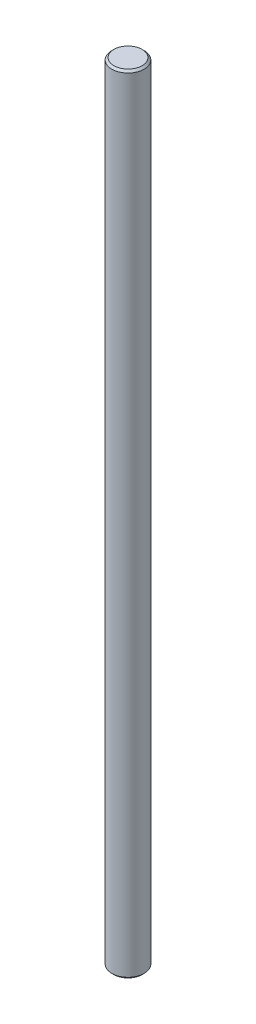
SolidWorks part; units mm, degrees
ref_plane "Front Plane" through (0, 0, 0) normal (0, 0, 1) x (1, 0, 0)
ref_plane "Top Plane" through (0, 0, 0) normal (0, 1, 0) x (1, 0, 0)
ref_plane "Right Plane" through (0, 0, 0) normal (1, 0, 0) x (0, 0, -1)
sketch "Sketch1" plane through (0, 0, 0) normal (0, 1, 0) x (1, 0, 0)
  circle A0 centre (0, 0) radius 4
  dimension "D1" = 8
extrude "Boss-Extrude1" add sketch "Sketch1" along normal mid plane 195
chamfer "Chamfer1" distance 0.5 angle 45 2 edges at (0, -97.5, 4) (0, 97.5, 4)
